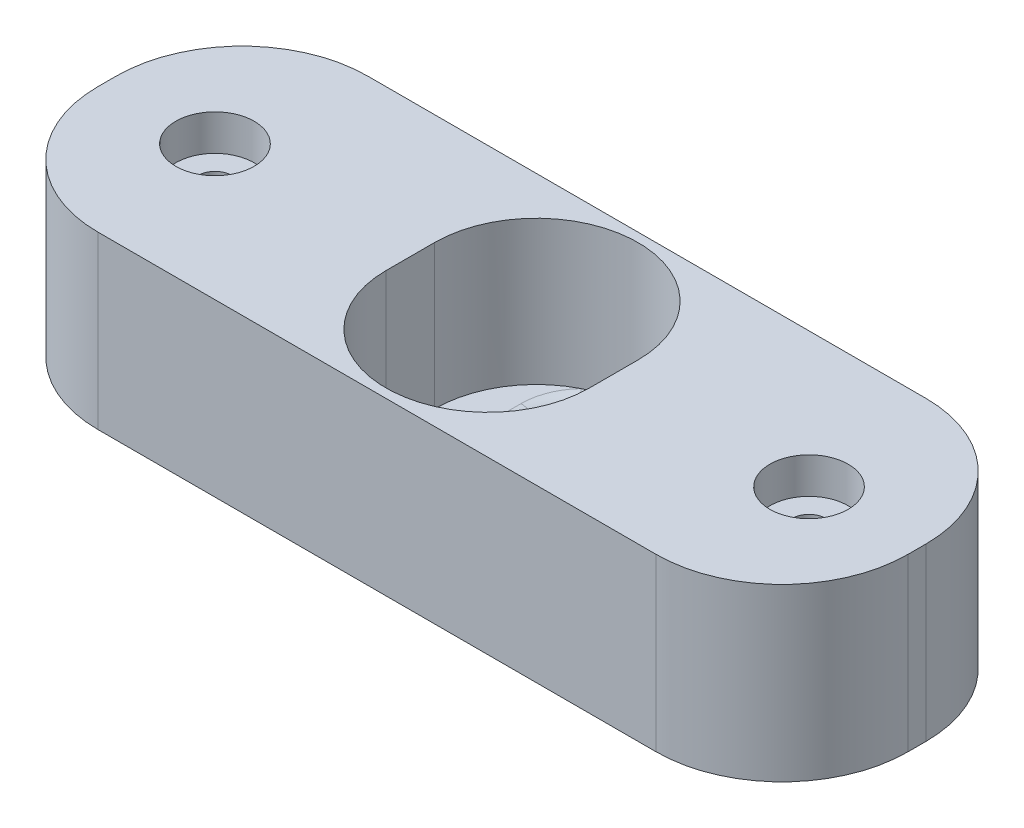
SolidWorks part; units mm, degrees
ref_plane "Front Plane" through (0, 0, 0) normal (0, 0, 1) x (1, 0, 0)
ref_plane "Top Plane" through (0, 0, 0) normal (0, 1, 0) x (1, 0, 0)
ref_plane "Right Plane" through (0, 0, 0) normal (1, 0, 0) x (0, 0, -1)
sketch "Sketch1" plane through (0, 0, 0) normal (0, 1, 0) x (1, 0, 0)
  line L1 (0, 0) -> (45, 0)
  line L2 (0, 0) -> (0, 15)
  line L3 (0, 15) -> (45, 15)
  line L4 (45, 0) -> (45, 15)
  dimension "D1" = 45
  dimension "D2" = 15
extrude "Boss-Extrude1" add sketch "Sketch1" against normal blind 9.5
sketch "Sketch8" plane through (0, 0, 0) normal (0, 1, 0) x (1, 0, 0)
  line L0 (45, 15) -> (0, 0) construction
  line L1 (0, 15) -> (45, 0) construction
  line L2 (45, 8.85) -> (0, 8.85) construction
  line L3 (45, 0) -> (45, 15) construction
  line L4 (0, 15) -> (0, 0) construction
  line L5 (0, 6.15) -> (45, 6.15) construction
  line L6 (22.5, 0) -> (22.5, 6.15) construction
  line L7 (0, 0) -> (45, 0) construction
  line L8 (22.5, 15) -> (22.5, 8.85) construction
  line L9 (45, 15) -> (0, 15) construction
  line L10 (16.85, 8.85) -> (16.85, 6.15)
  line L11 (28.15, 8.85) -> (28.15, 6.15)
  line L12 (22.5, 7.5) -> (16.85, 7.5) construction
  line L13 (22.5, 7.5) -> (28.15, 7.5) construction
  arc A0 (28.15, 8.85) -> (16.85, 8.85) centre (22.5, 8.85) ccw
  arc A1 (16.85, 6.15) -> (28.15, 6.15) centre (22.5, 6.15) ccw
  dimension "D1" = 6.15
  dimension "D2" = 5.65
sketch "Sketch2" plane through (0, 0, 0) normal (0, 1, 0) x (1, 0, 0)
  line L0 (45, 15) -> (0, 15) construction
  line L1 (0, 15) -> (0, 0) construction
  circle A0 centre (22.5, 8.82) radius 5.5
  dimension "D2" = 11
  dimension "D1" = 6.18
  dimension "D3" = 22.5
extrude "Cut-Extrude1" cut sketch "Sketch2" against normal blind 8
extrude "Cut-Extrude6" cut sketch "Sketch8" against normal blind 8
sketch "Sketch3" plane through (0, -8, 0) normal (0, 1, 0) x (1, 0, 0)
  line L0 (45, 15) -> (0, 0) construction
  line L3 (0, 15) -> (45, 0) construction
  line L4 (45, 11.5) -> (0, 11.5) construction
  line L5 (0, 3.5) -> (45, 3.5) construction
  line L6 (22.5, 0) -> (22.5, 3.5) construction
  line L7 (22.5, 15) -> (22.5, 11.5) construction
  line L8 (20, 11.5) -> (20, 3.5)
  line L9 (25, 11.5) -> (25, 3.5)
  line L10 (22.5, 7.5) -> (20, 7.5) construction
  line L11 (22.5, 7.5) -> (25, 7.5) construction
  line L12 (0, 15) -> (0, 0) construction
  line L13 (45, 15) -> (0, 15) construction
  arc A1 (25, 11.5) -> (20, 11.5) centre (22.5, 11.5) ccw
  arc A2 (20, 3.5) -> (25, 3.5) centre (22.5, 3.5) ccw
  point P42 (22.5, 15)
  dimension "D1" = 2.5
  dimension "D2" = 3.5
extrude "Cut-Extrude2" cut sketch "Sketch3" against normal up to next
sketch "Sketch4" plane through (0, 0, 0) normal (0, 1, 0) x (1, 0, 0)
  line L1 (6, 7.5) -> (22.5, 7.5) construction
  line L2 (22.5, 7.5) -> (39, 7.5) construction
  line L3 (22.5, 14) -> (22.5, 1) construction
  circle A0 centre (6, 7.5) radius 2.175
  circle A1 centre (39, 7.5) radius 2.175
  arc A4 (25, 11.5) -> (20, 11.5) centre (22.5, 11.5) ccw construction
  arc A5 (20, 3.5) -> (25, 3.5) centre (22.5, 3.5) ccw construction
  point P10 (0, 0)
  dimension "D3" = 4.35
  dimension "D4" = 16.5
extrude "Cut-Extrude3" cut sketch "Sketch4" against normal blind 2
fillet "Fillet1" radius 7 4 edges at (45, -4.75, -15) (0, -4.75, -15) (45, -4.75, 0) (0, -4.75, 0)
sketch "Sketch5" plane through (0, -9.5, 0) normal (0, -1, 0) x (-1, 0, 0)
  line L1 (-22.5, 1) -> (-22.5, 14) construction
  line L2 (-6, 7.5) -> (-22.5, 7.5) construction
  line L3 (-22.5, 7.5) -> (-39, 7.5) construction
  circle A0 centre (-39, 7.5) radius 2.05
  circle A1 centre (-6, 7.5) radius 2.05
  arc A3 (-25, 3.5) -> (-20, 3.5) centre (-22.5, 3.5) ccw construction
  arc A4 (-20, 11.5) -> (-25, 11.5) centre (-22.5, 11.5) ccw construction
  point P21 (-22.5, 7.5)
  dimension "D5" = 4.1
  dimension "D3" = 16.5
extrude "Cut-Extrude4" cut sketch "Sketch5" against normal blind 5
sketch "Sketch6" plane through (0, -2, 0) normal (0, 1, 0) x (1, 0, 0)
  circle A1 centre (6, 7.5) radius 0.95
  circle A2 centre (39, 7.5) radius 0.95
  circle A3 centre (6, 7.5) radius 2.175 construction
  circle A4 centre (39, 7.5) radius 2.175 construction
  point P5 (9.8937, 9.1408)
  point P6 (-2.1411, 9.935)
  dimension "D1" = 1.9
extrude "Cut-Extrude5" cut sketch "Sketch6" against normal blind 3
fillet "Fillet3" radius 1 4 edges at (22.5, -8, -14) (25, -8, -7.5) (22.5, -8, -1) (20, -8, -7.5)
